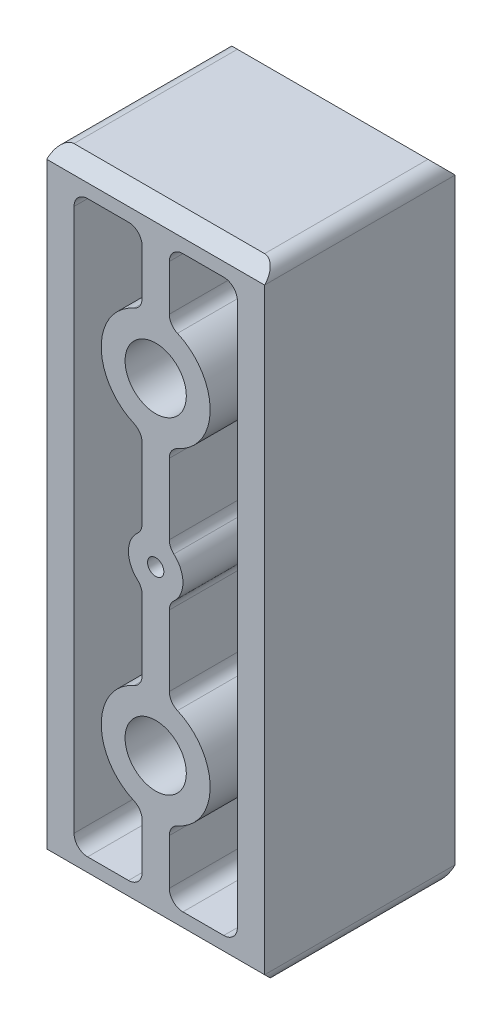
SolidWorks part; units mm, degrees
material "6061-T6 (SS)"
ref_plane "Front Plane" through (0, 0, 0) normal (0, 0, 1) x (1, 0, 0)
ref_plane "Top Plane" through (0, 0, 0) normal (0, 1, 0) x (1, 0, 0)
ref_plane "Right Plane" through (0, 0, 0) normal (1, 0, 0) x (0, 0, -1)
sketch "Sketch1" plane through (0, 0, 0) normal (0, 0, 1) x (1, 0, 0)
  line L0 (-25.4, 72.8218) -> (25.4, -72.8218) construction
  line L1 (-25.4, 72.8218) -> (25.4, 72.8218)
  line L2 (-25.4, 72.8218) -> (-25.4, -72.8218)
  line L3 (-25.4, -72.8218) -> (25.4, -72.8218)
  line L4 (25.4, 72.8218) -> (25.4, -72.8218)
  line L5 (0, 0) -> (47.3757, 0) construction
  line L6 (0, 38.1) -> (0, -38.1) construction
  line L11 (-25.4, 72.8218) -> (-25.4, -72.8218) construction
  circle A0 centre (0, 38.1) radius 7.1438
  circle A1 centre (0, -38.1) radius 7.1438
  point P4 (0, 0)
  point P10 (0, 0)
  point P15 (-25.4, 0)
  dimension "D6" = 14.2875
  dimension "D1" = 145.6436
  dimension "D2" = 50.8
  dimension "D3" = 76.2
extrude "Boss-Extrude1" add sketch "Sketch1" along normal mid plane 44.45
sketch "Sketch3" plane through (0, 0, 22.225) normal (0, 0, 1) x (1, 0, 0)
  line L1 (3.175, 53.2697) -> (-3.175, 53.2697) construction
  line L2 (15.0052, 72.8218) -> (15.0052, 66.4718) construction
  line L3 (25.4, 72.8218) -> (-25.4, 72.8218) construction
  line L4 (19.05, 66.4718) -> (19.05, 0)
  line L5 (19.05, 56.4161) -> (25.4, 56.4161) construction
  line L7 (3.175, 66.4718) -> (19.05, 66.4718)
  line L8 (25.4, -72.8218) -> (25.4, 72.8218) construction
  line L9 (6.35, 0) -> (19.05, 0)
  line L10 (-3.175, 0) -> (3.175, 0) construction
  line L12 (0, 0) -> (0, 63.5) construction
  line L15 (3.175, 66.4718) -> (3.175, 50.3967)
  line L19 (3.175, 25.8033) -> (3.175, 5.4993)
  arc A0 (6.35, 0) -> (3.175, 5.4993) centre (0, 0) ccw
  arc A1 (3.175, 50.3967) -> (3.175, 25.8033) centre (0, 38.1) cw
  point P4 (0, 0)
  point P17 (0, 53.2697)
  dimension "D3" = 12.7
  dimension "D2" = 38.1
  dimension "D4" = 12.7
  dimension "D1" = 6.35
  dimension "D5" = 63.5
extrude "Cut-Extrude2" cut sketch "Sketch3" against normal through all
mirror "Mirror4" about plane through (0, 0, 0) normal (1, 0, 0) of "Cut-Extrude2"
mirror "Mirror1" about plane through (0, 0, 0) normal (0, 1, 0) of "Cut-Extrude2"
fillet "Fillet1" radius 3.175 9 edges at (25.4, -72.8218, 0) (19.05, -66.4718, 0) (19.05, 66.4718, 0) (25.4, 72.8218, 0) (-25.4, -72.8218, 0) (-25.4, 72.8218, 0) (-3.175, 50.3967, 0) (3.175, 50.3967, 0) (-19.05, 66.4718, 0)
sketch "Sketch5" plane through (25.4, 0, 0) normal (1, 0, 0) x (0, 0, -1)
  line L0 (19.05, 72.8218) -> (22.225, 69.6468)
  line L2 (19.05, 72.8218) -> (22.225, 72.8218)
  line L3 (22.225, -69.6468) -> (22.225, 69.6468) construction
  line L4 (22.225, 69.6468) -> (22.225, 72.8218)
  line L5 (-22.225, 72.8218) -> (22.225, 72.8218) construction
  dimension "D1" = 45
extrude "Cut-Extrude4" cut sketch "Sketch5" against normal through all
mirror "Mirror2" about plane through (0, 0, 0) normal (0, 0, 1) of "Cut-Extrude4"
mirror "Mirror3" about plane through (0, 0, 0) normal (0, 1, 0) of "Mirror4", "Mirror2", "Cut-Extrude4"
hole_wizard "#10-24 Tapped Hole1" positions "Sketch9" profile "Sketch8" tap size "#10-24" standard "Ansi Inch"
sketch "Sketch9" plane through (0, 0, 22.225) normal (0, 0, 1) x (1, 0, 0)
  point P0 (0, 0)
sketch "Sketch8" plane through (0, 0, 22.225) normal (1, 0, 0) x (0, -1, 0)
  line L0 (0, 0) -> (0, 16.1268)
  line L1 (0, 16.1268) -> (1.8986, 14.986)
  line L2 (1.8986, 14.986) -> (1.8986, 0)
  line L5 (1.8986, 0) -> (0, 0)
  line L10 (0, 16.1268) -> (-1.8987, 14.986) construction
  line L11 (0, -6.35) -> (0, 107.95) construction
  dimension "Tap Drill Dia." = 3.7973
  dimension "Tap Drill Depth" = 14.986
  dimension "Drill Angle" = 118
cosmetic thread "Hole Thread2" parameters "D1"=9.652, "D2"=4.826
fillet "Fillet2" radius 3.175 16 edges at (-3.175, 66.4718, 0) (3.175, 66.4718, 0) (-19.05, -66.4718, 0) (-3.175, -66.4718, 0) (19.05, -66.4718, 0) (3.175, -66.4718, 0) (-3.175, -50.3967, 0) (3.175, -50.3967, 0) (3.175, -25.8033, 0) (-3.175, -25.8033, 0) (-3.175, -5.4993, 0) (-3.175, 25.8033, 0) (-3.175, 5.4993, 0) (3.175, 5.4993, 0) (3.175, -5.4993, 0) (3.175, 25.8033, 0)
